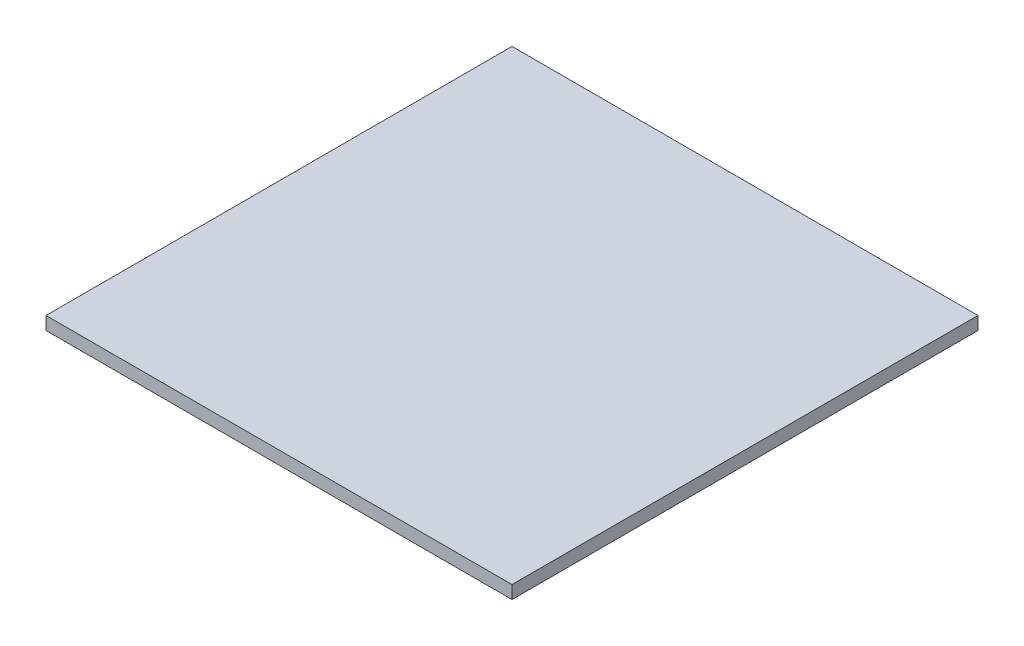
SolidWorks part; units mm, degrees
material "Acrylic (Medium-high impact)"
ref_plane "Front Plane" through (0, 0, 0) normal (0, 0, 1) x (1, 0, 0)
ref_plane "Top Plane" through (0, 0, 0) normal (0, 1, 0) x (1, 0, 0)
ref_plane "Right Plane" through (0, 0, 0) normal (1, 0, 0) x (0, 0, -1)
sketch "Sketch1" plane through (0, 0, 0) normal (0, 1, 0) x (1, 0, 0)
  line L1 (-12.5, -12.5) -> (12.5, -12.5)
  line L2 (-12.5, -12.5) -> (-12.5, 12.5)
  line L3 (-12.5, 12.5) -> (12.5, 12.5)
  line L4 (12.5, -12.5) -> (12.5, 12.5)
  line L5 (-12.5, -12.5) -> (12.5, 12.5) construction
  line L6 (-12.5, 12.5) -> (12.5, -12.5) construction
  point P0 (0, 0)
  dimension "D1" = 25
extrude "Boss-Extrude1" add sketch "Sketch1" along normal mid plane 0.7
